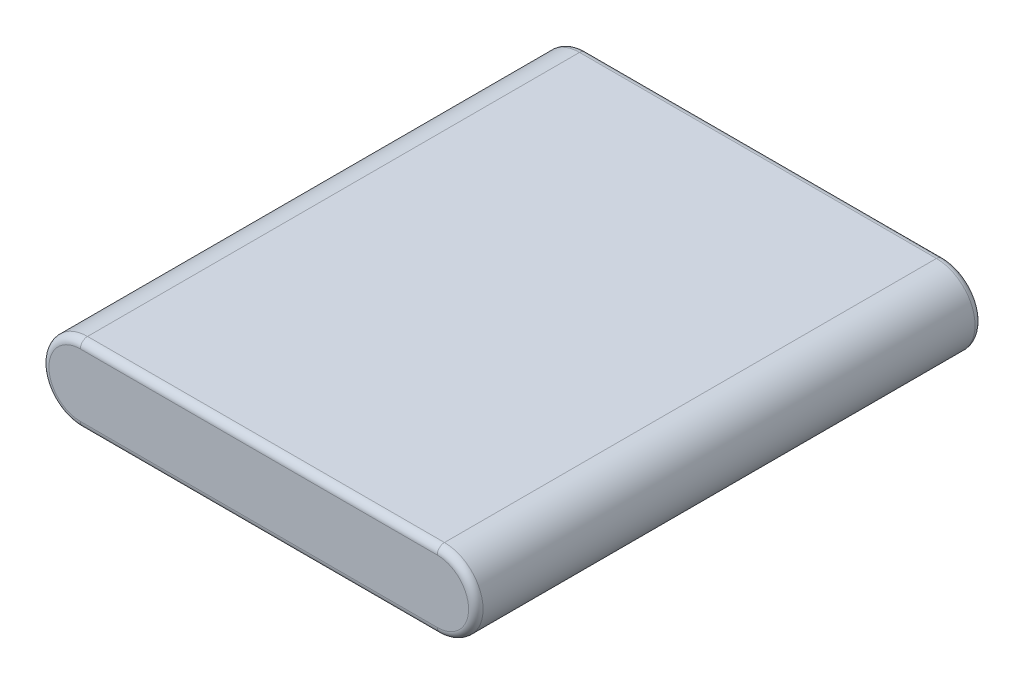
SolidWorks part; units mm, degrees
ref_plane "Front Plane" through (0, 0, 0) normal (0, 0, 1) x (1, 0, 0)
ref_plane "Top Plane" through (0, 0, 0) normal (0, 1, 0) x (1, 0, 0)
ref_plane "Right Plane" through (0, 0, 0) normal (1, 0, 0) x (0, 0, -1)
sketch "Sketch1" plane through (0, 0, 0) normal (0, 0, 1) x (1, 0, 0)
  line L0 (37, 0) -> (-37, 0) construction
  line L1 (37, -8) -> (-37, -8)
  line L2 (37, 8) -> (-37, 8)
  arc A0 (37, -8) -> (37, 8) centre (37, 0) ccw
  arc A1 (-37, 8) -> (-37, -8) centre (-37, 0) ccw
  point P3 (0, 0)
  dimension "D1" = 8
  dimension "D2" = 74
extrude "Extrude1" add sketch "Sketch1" along normal mid plane 105
fillet "Fillet1" radius 1.5 8 edges at (0, 8, -52.5) (-45, 0, -52.5) (0, -8, -52.5) (45, 0, -52.5) (0, -8, 52.5) (-45, 0, 52.5) (0, 8, 52.5) (45, 0, 52.5)
